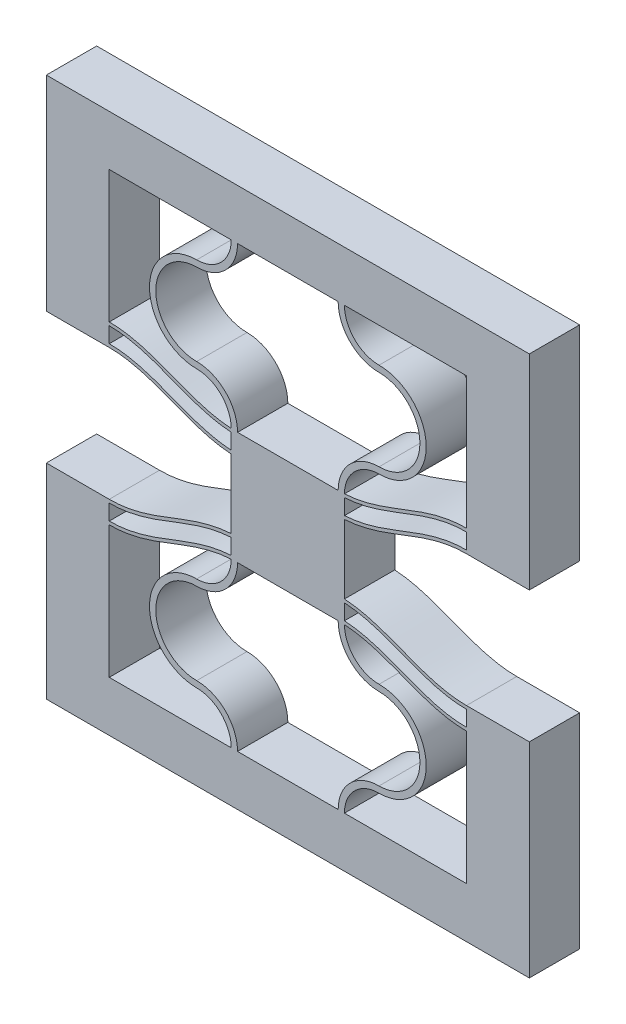
SolidWorks part; units mm, degrees
ref_plane "Front Plane" through (0, 0, 0) normal (0, 0, 1) x (1, 0, 0)
ref_plane "Top Plane" through (0, 0, 0) normal (0, 1, 0) x (1, 0, 0)
ref_plane "Right Plane" through (0, 0, 0) normal (1, 0, 0) x (0, 0, -1)
sketch "Sketch1" plane through (0, 0, 0) normal (0, 0, 1) x (1, 0, 0)
  line L4 (0, 10.5) -> (0, 0)
  line L5 (10.2, 0) -> (10.2, 13) construction
  line L6 (10.2, 13) -> (10.2, 15.9852) construction
  line L17 (9.7, 0) -> (0, 0)
  line L18 (10.7, 0) -> (20.4, 0)
  line L19 (20.4, 0) -> (20.4, 10.5)
  line L20 (10.7, 13.2452) -> (10.7, 14.4852)
  line L21 (9.7, 13.2452) -> (9.7, 14.4852)
  line L22 (10.7, 14.7452) -> (10.7, 15.9852)
  line L23 (10.7, 15.9852) -> (9.7, 15.9852)
  line L24 (9.7, 15.9852) -> (9.7, 14.7452)
  line L31 (-5, 12.26) -> (-5, -4)
  line L32 (-5, -4) -> (25.4, -4)
  line L33 (25.4, -4) -> (25.4, 12.26)
  line L34 (0, 10.76) -> (0, 12)
  line L36 (-5, 12.26) -> (0, 12.26)
  line L37 (25.4, 12.26) -> (20.4, 12.26)
  line L38 (20.4, 10.76) -> (20.4, 12)
  arc A0 (10.2, 13) -> (6.95, 9.75) centre (6.95, 13) cw
  arc A1 (6.95, 9.75) -> (6.95, 3.25) centre (6.95, 6.5) ccw
  arc A2 (6.95, 3.25) -> (10.2, 0) centre (6.95, 0) cw
  arc A3 (9.7, 12.9852) -> (6.95, 10.25) centre (6.95, 13) cw
  arc A4 (6.95, 10.25) -> (6.95, 2.75) centre (6.95, 6.5) ccw
  arc A5 (6.95, 2.75) -> (9.7, 0) centre (6.95, 0) cw
  arc A6 (9.7, 13) -> (6.95, 10.25) centre (6.95, 13) cw construction
  arc A7 (13.45, 3.25) -> (10.2, 0) centre (13.45, 0) ccw
  arc A8 (13.45, 2.75) -> (10.7, 0) centre (13.45, 0) ccw
  arc A9 (13.45, 9.75) -> (13.45, 3.25) centre (13.45, 6.5) cw
  arc A10 (13.45, 10.25) -> (13.45, 2.75) centre (13.45, 6.5) cw
  arc A11 (10.7, 12.9852) -> (13.45, 10.25) centre (13.45, 13) ccw
  arc A12 (10.2, 13) -> (13.45, 9.75) centre (13.45, 13) ccw
  spline S0 degree 4 poles (-2.0399, 10.9987) (-1.9769, 10.9844) (-1.8506, 10.9568) (-1.6594, 10.9185) (-1.4063, 10.8738) (-1.1473, 10.836) (-0.8994, 10.8056) (-0.6275, 10.7825) (-0.4084, 10.7671) (-0.0945, 10.7598) (0.0489, 10.7593) (0.3554, 10.7653) (0.5833, 10.7785) (0.8327, 10.7992) (1.1232, 10.8326) (1.4148, 10.8743) (1.7521, 10.9345) (2.2064, 11.0333) (2.726, 11.1697) (3.2397, 11.3281) (3.7479, 11.5024) (4.1845, 11.6613) (4.5513, 11.7992) (4.9172, 11.9395) (5.2828, 12.0805) (5.7402, 12.2559) (6.427, 12.5125) (7.2136, 12.7819) (8.1107, 13.0284) (9.0261, 13.1932) (9.8075, 13.2661) (10.5925, 13.2661) (11.3739, 13.1932) (12.2893, 13.0284) (13.1864, 12.7819) (13.973, 12.5125) (14.6598, 12.2559) (15.2087, 12.0455) (15.6656, 11.8688) (16.1235, 11.6948) (16.6521, 11.5024) (17.1603, 11.3281) (17.6739, 11.1697) (18.1937, 11.0333) (18.5999, 10.9449) (18.8889, 10.8915) (19.1309, 10.8534) (19.3251, 10.827) (19.5196, 10.8048) (19.7158, 10.7868) (19.909, 10.7733) (20.1017, 10.7642) (20.3513, 10.7593) (20.4943, 10.7598) (20.8085, 10.7671) (21.0274, 10.7825) (21.2994, 10.8056) (21.5473, 10.836) (21.8063, 10.8738) (22.0594, 10.9185) (22.2506, 10.9568) (22.3769, 10.9844) (22.4399, 10.9987) knots 0 0 0 0 0 0.010251 0.020502 0.030753 0.041005 0.05113 0.061255 0.071381 0.081506 0.089265 0.097024 0.112543 0.120302 0.128061 0.143579 0.159098 0.174616 0.201648 0.22868 0.244198 0.259716 0.275235 0.290753 0.306271 0.32179 0.352826 0.40689 0.437927 0.468963 0.5 0.531037 0.562073 0.59311 0.647174 0.67821 0.693729 0.709247 0.740284 0.755802 0.77132 0.798352 0.825384 0.840902 0.856421 0.86418 0.871939 0.879698 0.887457 0.895217 0.902976 0.910735 0.918494 0.928619 0.938745 0.94887 0.958995 0.969247 0.979498 0.989749 1 1 1 1 1 construction
  spline S1 degree 4 poles (0, 10.76) (0.041, 10.76) (0.1243, 10.7608) (0.3554, 10.7653) (0.5833, 10.7785) (0.8327, 10.7992) (1.1232, 10.8326) (1.4148, 10.8743) (1.7521, 10.9345) (2.2064, 11.0333) (2.726, 11.1697) (3.2397, 11.3281) (3.7479, 11.5024) (4.1845, 11.6613) (4.5513, 11.7992) (4.9172, 11.9395) (5.2828, 12.0805) (5.7402, 12.2559) (6.427, 12.5125) (7.2136, 12.7819) (8.1107, 13.0284) (9.0261, 13.1932) (9.8075, 13.2661) (10.5925, 13.2661) (11.3739, 13.1932) (12.2893, 13.0284) (13.1864, 12.7819) (13.973, 12.5125) (14.6598, 12.2559) (15.2087, 12.0455) (15.6656, 11.8688) (16.1235, 11.6948) (16.6521, 11.5024) (17.1603, 11.3281) (17.6739, 11.1697) (18.1937, 11.0333) (18.5999, 10.9449) (18.8889, 10.8915) (19.1309, 10.8534) (19.3251, 10.827) (19.5196, 10.8048) (19.7158, 10.7868) (19.909, 10.7733) (20.1017, 10.7642) (20.2757, 10.7608) (20.359, 10.76) (20.4, 10.76) knots 0.081506 0.081506 0.081506 0.081506 0.081506 0.089265 0.097024 0.112543 0.120302 0.128061 0.143579 0.159098 0.174616 0.201648 0.22868 0.244198 0.259716 0.275235 0.290753 0.306271 0.32179 0.352826 0.40689 0.437927 0.468963 0.5 0.531037 0.562073 0.59311 0.647174 0.67821 0.693729 0.709247 0.740284 0.755802 0.77132 0.798352 0.825384 0.840902 0.856421 0.86418 0.871939 0.879698 0.887457 0.895217 0.902976 0.910735 0.918494 0.918494 0.918494 0.918494 0.918494
  spline S2 degree 4 poles (-2.0399, 12.2387) (-1.9769, 12.2244) (-1.8506, 12.1968) (-1.6594, 12.1585) (-1.4063, 12.1138) (-1.1473, 12.076) (-0.8994, 12.0456) (-0.6275, 12.0225) (-0.4084, 12.0071) (-0.0945, 11.9998) (0.0489, 11.9993) (0.3554, 12.0053) (0.5833, 12.0185) (0.8327, 12.0392) (1.1232, 12.0726) (1.4148, 12.1143) (1.7521, 12.1745) (2.2064, 12.2733) (2.726, 12.4097) (3.2397, 12.5681) (3.7479, 12.7424) (4.1845, 12.9013) (4.5513, 13.0392) (4.9172, 13.1795) (5.2828, 13.3205) (5.7402, 13.4959) (6.427, 13.7525) (7.2136, 14.0219) (8.1107, 14.2684) (9.0261, 14.4332) (9.8075, 14.5061) (10.5925, 14.5061) (11.3739, 14.4332) (12.2893, 14.2684) (13.1864, 14.0219) (13.973, 13.7525) (14.6598, 13.4959) (15.2087, 13.2855) (15.6656, 13.1088) (16.1235, 12.9348) (16.6521, 12.7424) (17.1603, 12.5681) (17.6739, 12.4097) (18.1937, 12.2733) (18.5999, 12.1849) (18.8889, 12.1315) (19.1309, 12.0934) (19.3251, 12.067) (19.5196, 12.0448) (19.7158, 12.0268) (19.909, 12.0133) (20.1017, 12.0042) (20.3513, 11.9993) (20.4943, 11.9998) (20.8085, 12.0071) (21.0274, 12.0225) (21.2994, 12.0456) (21.5473, 12.076) (21.8063, 12.1138) (22.0594, 12.1585) (22.2506, 12.1968) (22.3769, 12.2244) (22.4399, 12.2387) knots 0 0 0 0 0 0.010251 0.020502 0.030753 0.041005 0.05113 0.061255 0.071381 0.081506 0.089265 0.097024 0.112543 0.120302 0.128061 0.143579 0.159098 0.174616 0.201648 0.22868 0.244198 0.259716 0.275235 0.290753 0.306271 0.32179 0.352826 0.40689 0.437927 0.468963 0.5 0.531037 0.562073 0.59311 0.647174 0.67821 0.693729 0.709247 0.740284 0.755802 0.77132 0.798352 0.825384 0.840902 0.856421 0.86418 0.871939 0.879698 0.887457 0.895217 0.902976 0.910735 0.918494 0.928619 0.938745 0.94887 0.958995 0.969247 0.979498 0.989749 1 1 1 1 1 construction
  spline S3 degree 4 poles (0, 12) (0.041, 12) (0.1243, 12.0008) (0.3554, 12.0053) (0.5833, 12.0185) (0.8327, 12.0392) (1.1232, 12.0726) (1.4148, 12.1143) (1.7521, 12.1745) (2.2064, 12.2733) (2.726, 12.4097) (3.2397, 12.5681) (3.7479, 12.7424) (4.1845, 12.9013) (4.5513, 13.0392) (4.9172, 13.1795) (5.2828, 13.3205) (5.7402, 13.4959) (6.427, 13.7525) (7.2136, 14.0219) (8.1107, 14.2684) (9.0261, 14.4332) (9.8075, 14.5061) (10.5925, 14.5061) (11.3739, 14.4332) (12.2893, 14.2684) (13.1864, 14.0219) (13.973, 13.7525) (14.6598, 13.4959) (15.2087, 13.2855) (15.6656, 13.1088) (16.1235, 12.9348) (16.6521, 12.7424) (17.1603, 12.5681) (17.6739, 12.4097) (18.1937, 12.2733) (18.5999, 12.1849) (18.8889, 12.1315) (19.1309, 12.0934) (19.3251, 12.067) (19.5196, 12.0448) (19.7158, 12.0268) (19.909, 12.0133) (20.1017, 12.0042) (20.2757, 12.0008) (20.359, 12) (20.4, 12) knots 0.081506 0.081506 0.081506 0.081506 0.081506 0.089265 0.097024 0.112543 0.120302 0.128061 0.143579 0.159098 0.174616 0.201648 0.22868 0.244198 0.259716 0.275235 0.290753 0.306271 0.32179 0.352826 0.40689 0.437927 0.468963 0.5 0.531037 0.562073 0.59311 0.647174 0.67821 0.693729 0.709247 0.740284 0.755802 0.77132 0.798352 0.825384 0.840902 0.856421 0.86418 0.871939 0.879698 0.887457 0.895217 0.902976 0.910735 0.918494 0.918494 0.918494 0.918494 0.918494
  spline S4 degree 4 poles (-2.0399, 12.4987) (-1.9769, 12.4844) (-1.8506, 12.4568) (-1.6594, 12.4185) (-1.4063, 12.3738) (-1.1473, 12.336) (-0.8994, 12.3056) (-0.6275, 12.2825) (-0.4084, 12.2671) (-0.0945, 12.2598) (0.0489, 12.2593) (0.3554, 12.2653) (0.5833, 12.2785) (0.8327, 12.2992) (1.1232, 12.3326) (1.4148, 12.3743) (1.7521, 12.4345) (2.2064, 12.5333) (2.726, 12.6697) (3.2397, 12.8281) (3.7479, 13.0024) (4.1845, 13.1613) (4.5513, 13.2992) (4.9172, 13.4395) (5.2828, 13.5805) (5.7402, 13.7559) (6.427, 14.0125) (7.2136, 14.2819) (8.1107, 14.5284) (9.0261, 14.6932) (9.8075, 14.7661) (10.5925, 14.7661) (11.3739, 14.6932) (12.2893, 14.5284) (13.1864, 14.2819) (13.973, 14.0125) (14.6598, 13.7559) (15.2087, 13.5455) (15.6656, 13.3688) (16.1235, 13.1948) (16.6521, 13.0024) (17.1603, 12.8281) (17.6739, 12.6697) (18.1937, 12.5333) (18.5999, 12.4449) (18.8889, 12.3915) (19.1309, 12.3534) (19.3251, 12.327) (19.5196, 12.3048) (19.7158, 12.2868) (19.909, 12.2733) (20.1017, 12.2642) (20.3513, 12.2593) (20.4943, 12.2598) (20.8085, 12.2671) (21.0274, 12.2825) (21.2994, 12.3056) (21.5473, 12.336) (21.8063, 12.3738) (22.0594, 12.4185) (22.2506, 12.4568) (22.3769, 12.4844) (22.4399, 12.4987) knots 0 0 0 0 0 0.010251 0.020502 0.030753 0.041005 0.05113 0.061255 0.071381 0.081506 0.089265 0.097024 0.112543 0.120302 0.128061 0.143579 0.159098 0.174616 0.201648 0.22868 0.244198 0.259716 0.275235 0.290753 0.306271 0.32179 0.352826 0.40689 0.437927 0.468963 0.5 0.531037 0.562073 0.59311 0.647174 0.67821 0.693729 0.709247 0.740284 0.755802 0.77132 0.798352 0.825384 0.840902 0.856421 0.86418 0.871939 0.879698 0.887457 0.895217 0.902976 0.910735 0.918494 0.928619 0.938745 0.94887 0.958995 0.969247 0.979498 0.989749 1 1 1 1 1 construction
  spline S5 degree 4 poles (0, 12.26) (0.041, 12.26) (0.1243, 12.2608) (0.3554, 12.2653) (0.5833, 12.2785) (0.8327, 12.2992) (1.1232, 12.3326) (1.4148, 12.3743) (1.7521, 12.4345) (2.2064, 12.5333) (2.726, 12.6697) (3.2397, 12.8281) (3.7479, 13.0024) (4.1845, 13.1613) (4.5513, 13.2992) (4.9172, 13.4395) (5.2828, 13.5805) (5.7402, 13.7559) (6.427, 14.0125) (7.2136, 14.2819) (8.1107, 14.5284) (9.0261, 14.6932) (9.8075, 14.7661) (10.5925, 14.7661) (11.3739, 14.6932) (12.2893, 14.5284) (13.1864, 14.2819) (13.973, 14.0125) (14.6598, 13.7559) (15.2087, 13.5455) (15.6656, 13.3688) (16.1235, 13.1948) (16.6521, 13.0024) (17.1603, 12.8281) (17.6739, 12.6697) (18.1937, 12.5333) (18.5999, 12.4449) (18.8889, 12.3915) (19.1309, 12.3534) (19.3251, 12.327) (19.5196, 12.3048) (19.7158, 12.2868) (19.909, 12.2733) (20.1017, 12.2642) (20.2757, 12.2608) (20.359, 12.26) (20.4, 12.26) knots 0.081506 0.081506 0.081506 0.081506 0.081506 0.089265 0.097024 0.112543 0.120302 0.128061 0.143579 0.159098 0.174616 0.201648 0.22868 0.244198 0.259716 0.275235 0.290753 0.306271 0.32179 0.352826 0.40689 0.437927 0.468963 0.5 0.531037 0.562073 0.59311 0.647174 0.67821 0.693729 0.709247 0.740284 0.755802 0.77132 0.798352 0.825384 0.840902 0.856421 0.86418 0.871939 0.879698 0.887457 0.895217 0.902976 0.910735 0.918494 0.918494 0.918494 0.918494 0.918494
  spline S8 degree 4 poles (-2.0399, 10.7387) (-1.9769, 10.7244) (-1.8506, 10.6968) (-1.6594, 10.6585) (-1.4063, 10.6138) (-1.1473, 10.576) (-0.8994, 10.5456) (-0.6275, 10.5225) (-0.4084, 10.5071) (-0.0945, 10.4998) (0.0489, 10.4993) (0.3554, 10.5053) (0.5833, 10.5185) (0.8327, 10.5392) (1.1232, 10.5726) (1.4148, 10.6143) (1.7521, 10.6745) (2.2064, 10.7733) (2.726, 10.9097) (3.2397, 11.0681) (3.7479, 11.2424) (4.1845, 11.4013) (4.5513, 11.5392) (4.9172, 11.6795) (5.2828, 11.8205) (5.7402, 11.9959) (6.427, 12.2525) (7.2136, 12.5219) (8.1107, 12.7684) (9.0261, 12.9332) (9.8075, 13.0061) (10.5925, 13.0061) (11.3739, 12.9332) (12.2893, 12.7684) (13.1864, 12.5219) (13.973, 12.2525) (14.6598, 11.9959) (15.2087, 11.7855) (15.6656, 11.6088) (16.1235, 11.4348) (16.6521, 11.2424) (17.1603, 11.0681) (17.6739, 10.9097) (18.1937, 10.7733) (18.5999, 10.6849) (18.8889, 10.6315) (19.1309, 10.5934) (19.3251, 10.567) (19.5196, 10.5448) (19.7158, 10.5268) (19.909, 10.5133) (20.1017, 10.5042) (20.3513, 10.4993) (20.4943, 10.4998) (20.8085, 10.5071) (21.0274, 10.5225) (21.2994, 10.5456) (21.5473, 10.576) (21.8063, 10.6138) (22.0594, 10.6585) (22.2506, 10.6968) (22.3769, 10.7244) (22.4399, 10.7387) knots 0 0 0 0 0 0.010251 0.020502 0.030753 0.041005 0.05113 0.061255 0.071381 0.081506 0.089265 0.097024 0.112543 0.120302 0.128061 0.143579 0.159098 0.174616 0.201648 0.22868 0.244198 0.259716 0.275235 0.290753 0.306271 0.32179 0.352826 0.40689 0.437927 0.468963 0.5 0.531037 0.562073 0.59311 0.647174 0.67821 0.693729 0.709247 0.740284 0.755802 0.77132 0.798352 0.825384 0.840902 0.856421 0.86418 0.871939 0.879698 0.887457 0.895217 0.902976 0.910735 0.918494 0.928619 0.938745 0.94887 0.958995 0.969247 0.979498 0.989749 1 1 1 1 1 construction
  spline S9 degree 4 poles (0, 10.5) (0.041, 10.5) (0.1243, 10.5008) (0.3554, 10.5053) (0.5833, 10.5185) (0.8327, 10.5392) (1.1232, 10.5726) (1.4148, 10.6143) (1.7521, 10.6745) (2.2064, 10.7733) (2.726, 10.9097) (3.2397, 11.0681) (3.7479, 11.2424) (4.1845, 11.4013) (4.5513, 11.5392) (4.9172, 11.6795) (5.2828, 11.8205) (5.7402, 11.9959) (6.427, 12.2525) (7.2136, 12.5219) (8.1107, 12.7684) (9.0261, 12.9332) (9.8075, 13.0061) (10.5925, 13.0061) (11.3739, 12.9332) (12.2893, 12.7684) (13.1864, 12.5219) (13.973, 12.2525) (14.6598, 11.9959) (15.2087, 11.7855) (15.6656, 11.6088) (16.1235, 11.4348) (16.6521, 11.2424) (17.1603, 11.0681) (17.6739, 10.9097) (18.1937, 10.7733) (18.5999, 10.6849) (18.8889, 10.6315) (19.1309, 10.5934) (19.3251, 10.567) (19.5196, 10.5448) (19.7158, 10.5268) (19.909, 10.5133) (20.1017, 10.5042) (20.2757, 10.5008) (20.359, 10.5) (20.4, 10.5) knots 0.081506 0.081506 0.081506 0.081506 0.081506 0.089265 0.097024 0.112543 0.120302 0.128061 0.143579 0.159098 0.174616 0.201648 0.22868 0.244198 0.259716 0.275235 0.290753 0.306271 0.32179 0.352826 0.40689 0.437927 0.468963 0.5 0.531037 0.562073 0.59311 0.647174 0.67821 0.693729 0.709247 0.740284 0.755802 0.77132 0.798352 0.825384 0.840902 0.856421 0.86418 0.871939 0.879698 0.887457 0.895217 0.902976 0.910735 0.918494 0.918494 0.918494 0.918494 0.918494
  dimension "D4" = 0.26
  dimension "D6" = 4
  dimension "D1" = 13
  dimension "D2" = 0.5
  dimension "D3" = 0.26
  dimension "D7" = 5
  dimension "D5" = 1.5
extrude "Boss-Extrude1" add sketch "Sketch1" along normal blind 4
sketch "Sketch4" plane through (0, 15.9852, 0) normal (0, 1, 0) x (1, 0, 0)
  line L24 (10.7, 0) -> (9.7, 0)
  line L25 (9.7, 0) -> (9.7, -4)
  line L26 (10.7, 0) -> (9.7, 0)
  line L27 (10.7, -4) -> (10.7, 0)
  line L29 (9.7, 0) -> (9.7, -4)
  line L31 (10.7, -4) -> (10.7, 0)
  line L32 (9.7, -4) -> (10.7, -4)
  line L33 (9.7, -4) -> (10.7, -4)
  dimension "D1" = 0
extrude "Boss-Extrude2" add sketch "Sketch4" along normal blind 1.5
mirror "Mirror3" about plane through (0, 17.4852, 0) normal (0, 1, 0) of bodies 179
ref_plane "Plane1" through (10.2, 0, 0) normal (-1, 0, 0) x (0, 0, 1)
split "Split2" trim tools "Plane1" bodies to split 247 102 resulting bodies 225
sketch "Sketch7" plane through (10.2, 0, 0) normal (-1, 0, 0) x (0, 0, 1)
  line L4 (4, 34.9704) -> (4, 38.9704)
  line L12 (0, 13) -> (4, 13)
  line L13 (0, 13) -> (4, 13)
  line L14 (4, 13) -> (4, 21.9704)
  line L15 (4, 13) -> (4, 21.9704)
  line L20 (4, 0) -> (0, 0)
  line L22 (4, 0) -> (0, 0)
  line L23 (0, -4) -> (4, -4)
  line L27 (0, -4) -> (4, -4)
  line L31 (4, 21.9704) -> (0, 21.9704)
  line L32 (4, 21.9704) -> (0, 21.9704)
  line L33 (0, 21.9704) -> (0, 13)
  line L34 (0, 21.9704) -> (0, 13)
  line L36 (4, -4) -> (4, 0)
  line L38 (4, 34.9704) -> (4, 38.9704)
  line L39 (4, 34.9704) -> (4, 38.9704)
  line L40 (4, 38.9704) -> (0, 38.9704)
  line L41 (4, 38.9704) -> (0, 38.9704)
  line L46 (4, 34.9704) -> (4, 38.9704)
  line L51 (0, 38.9704) -> (0, 34.9704)
  line L52 (0, 38.9704) -> (0, 34.9704)
  line L53 (0, 34.9704) -> (4, 34.9704)
  line L54 (0, 34.9704) -> (4, 34.9704)
  line L55 (4, 38.9704) -> (0, 38.9704)
  line L57 (4, 38.9704) -> (0, 38.9704)
  line L59 (4, -4) -> (4, 0)
  line L60 (0, 0) -> (0, -4)
  line L61 (0, 0) -> (0, -4)
  line L62 (0, 38.9704) -> (0, 34.9704)
  line L63 (0, 38.9704) -> (0, 34.9704)
  line L64 (0, 34.9704) -> (4, 34.9704)
  line L65 (0, 34.9704) -> (4, 34.9704)
  dimension "D1" = 0
  dimension "D2" = 0
  dimension "D3" = 0
  dimension "D4" = 0
extrude "Boss-Extrude3" add sketch "Sketch7" along normal blind 4
mirror "Mirror2" about plane through (6.2, 0, 0) normal (-1, 0, 0) of bodies 226
